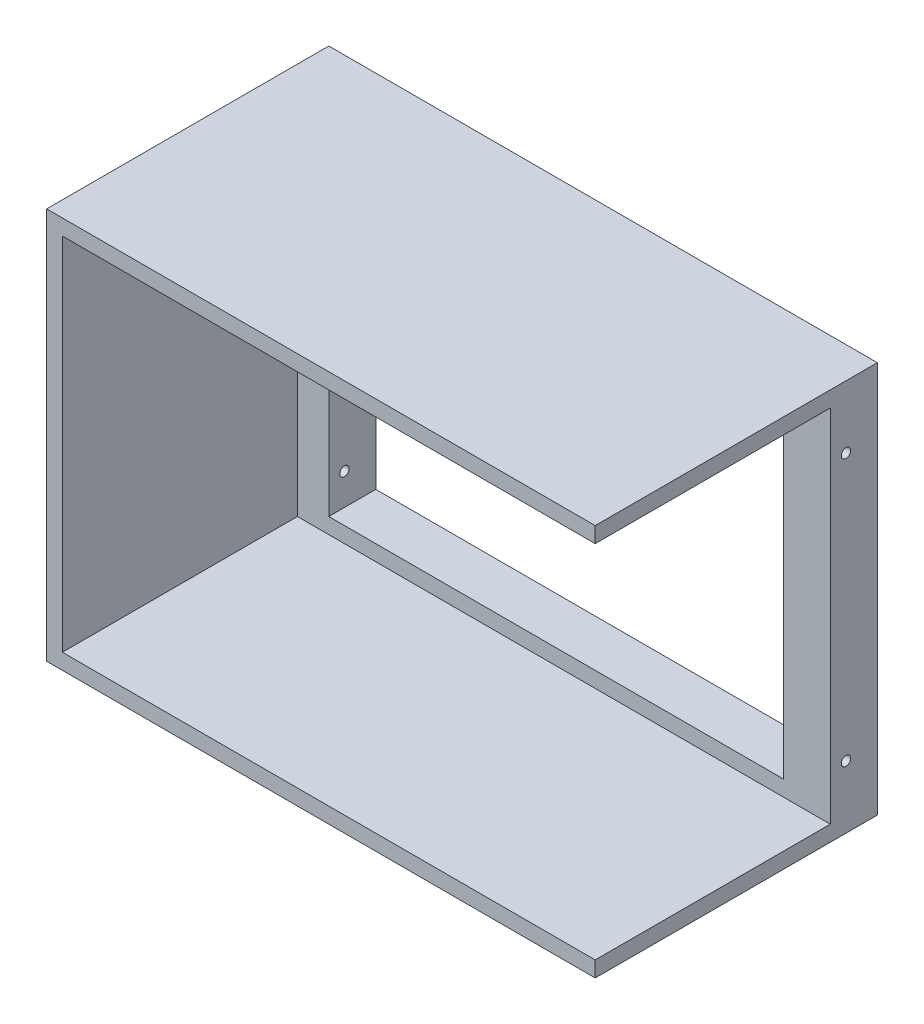
SolidWorks part; units mm, degrees
ref_plane "前视基准面" through (0, 0, 0) normal (0, 0, 1) x (1, 0, 0)
ref_plane "上视基准面" through (0, 0, 0) normal (0, 1, 0) x (1, 0, 0)
ref_plane "右视基准面" through (0, 0, 0) normal (1, 0, 0) x (0, 0, -1)
sketch "草图1" plane through (0, 0, 0) normal (0, 0, 1) x (1, 0, 0)
  line L1 (-175, -125) -> (175, -125)
  line L2 (-175, -125) -> (-175, 125)
  line L3 (-175, 125) -> (175, 125)
  line L4 (175, -125) -> (175, 125)
  line L5 (-175, -125) -> (175, 125) construction
  line L6 (-175, 125) -> (175, -125) construction
  point P0 (0, 0)
  dimension "D1" = 350
  dimension "D2" = 250
extrude "凸台-拉伸1" add sketch "草图1" along normal blind 30 contours L2 L3 L4 L1
sketch "草图2" plane through (0, 0, 30) normal (0, 0, 1) x (1, 0, 0)
  line L0 (175, -125) -> (175, 125) construction
  line L1 (-145, -105) -> (145, -105)
  line L2 (-145, -105) -> (-145, 105)
  line L3 (-145, 105) -> (145, 105)
  line L4 (145, -105) -> (145, 105)
  line L5 (-145, -105) -> (145, 105) construction
  line L6 (-145, 105) -> (145, -105) construction
  line L7 (-175, 125) -> (175, 125) construction
  point P0 (0, 0)
  dimension "D1" = 30
  dimension "D2" = 20
extrude "切除-拉伸1" cut sketch "草图2" against normal blind 30
sketch "草图3" plane through (175, 0, 0) normal (1, 0, 0) x (0, 0, -1)
  line L0 (0, 105) -> (-30, 105) construction
  line L1 (-30, -125) -> (-30, 125) construction
  circle A0 centre (-20, 85) radius 3
  dimension "D2" = 6
  dimension "D1" = 20
  dimension "D3" = 10
extrude "切除-拉伸2" cut sketch "草图3" against normal through all
mirror "镜向1" about plane through (0, 0, 0) normal (0, 1, 0) of "切除-拉伸2"
sketch "草图4" plane through (0, 0, 30) normal (0, 0, 1) x (1, 0, 0)
  line L1 (-175, 125) -> (175, 125)
  line L2 (-175, 125) -> (-175, -125)
  line L3 (-175, -125) -> (175, -125)
  line L4 (175, 125) -> (175, -125)
  line L5 (-165, 115) -> (165, 115)
  line L6 (-165, 115) -> (-165, -115)
  line L7 (-165, -115) -> (165, -115)
  line L8 (165, 115) -> (165, -115)
  dimension "D1" = 10
  dimension "D2" = 10
  dimension "D3" = 10
  dimension "D4" = 10
extrude "凸台-拉伸2" add sketch "草图4" along normal blind 150
sketch "草图5" plane through (0, 0, 180) normal (0, 0, 1) x (1, 0, 0)
  line L0 (175, -125) -> (175, 125) construction
  line L1 (165, 115) -> (175, 115)
  line L2 (165, 115) -> (165, -115)
  line L3 (165, -115) -> (175, -115)
  line L4 (175, 115) -> (175, -115)
  line L5 (-165, -115) -> (165, -115) construction
extrude "切除-拉伸3" cut sketch "草图5" against normal up to surface (150 mm away) up to face at (0, 0, 30)
